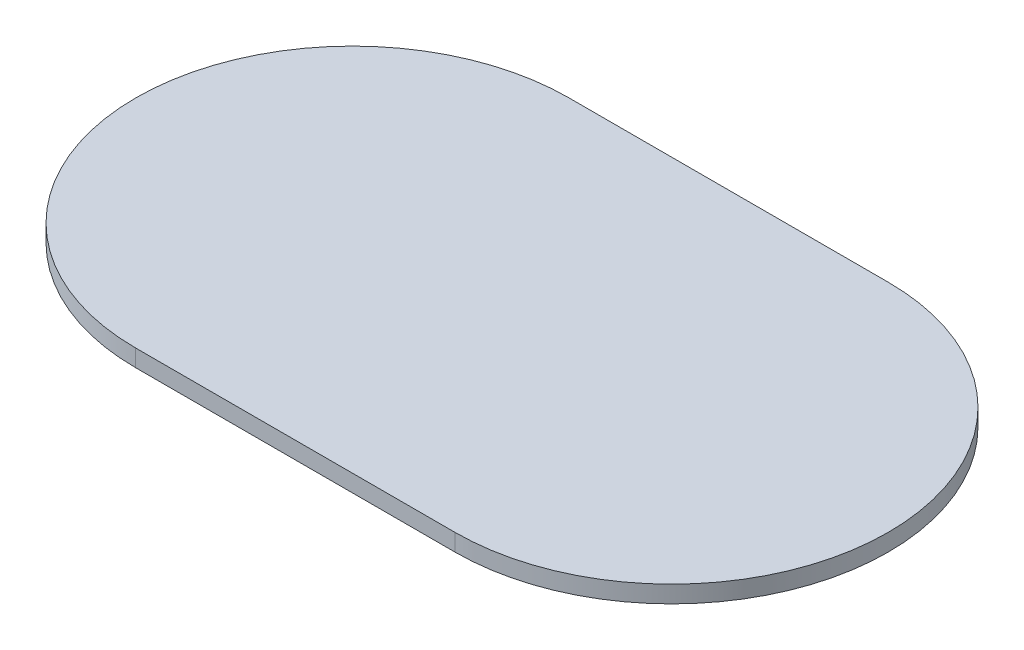
SolidWorks part; units mm, degrees
material "Mahogany"
ref_plane "Front Plane" through (0, 0, 0) normal (0, 0, 1) x (1, 0, 0)
ref_plane "Top Plane" through (0, 0, 0) normal (0, 1, 0) x (1, 0, 0)
ref_plane "Right Plane" through (0, 0, 0) normal (1, 0, 0) x (0, 0, -1)
sketch "Sketch2" plane through (0, 0, 0) normal (0, 1, 0) x (1, 0, 0)
  line L1 (-28, 38) -> (28, 38)
  line L3 (-28, -38) -> (28, -38)
  line L5 (-28, 38) -> (28, -38) construction
  line L6 (-28, -38) -> (28, 38) construction
  arc A0 (28, 38) -> (28, -38) centre (28, 0) cw
  arc A1 (-28, 38) -> (-28, -38) centre (-28, 0) ccw
  point P0 (0, 0)
  dimension "D1" = 76
  dimension "D2" = 56
extrude "Boss-Extrude1" add sketch "Sketch2" along normal blind 3
